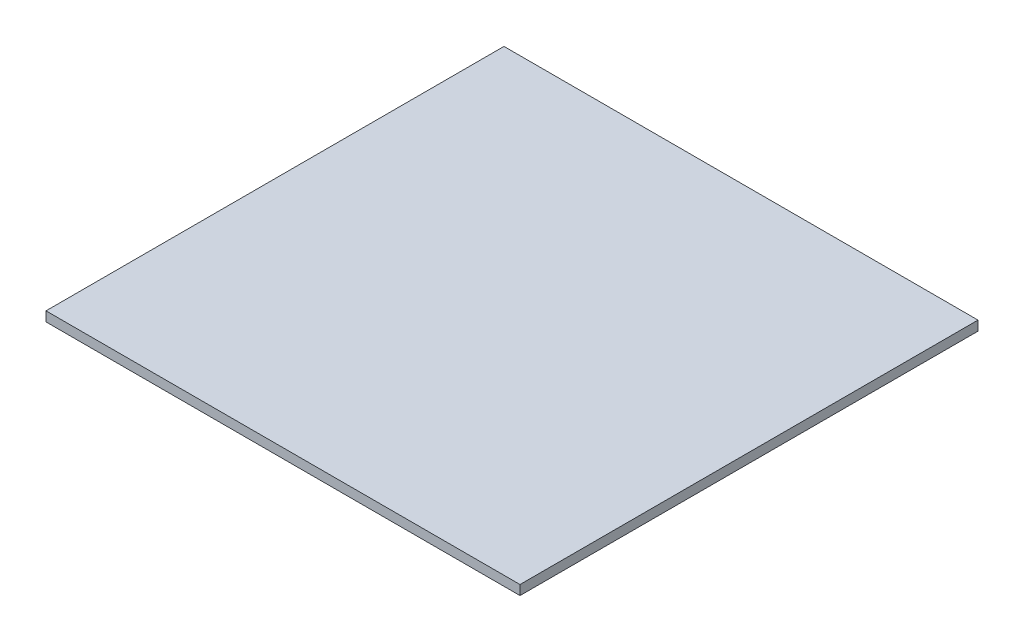
SolidWorks part; units mm, degrees
ref_plane "Front Plane" through (0, 0, 0) normal (0, 0, 1) x (1, 0, 0)
ref_plane "Top Plane" through (0, 0, 0) normal (0, 1, 0) x (1, 0, 0)
ref_plane "Right Plane" through (0, 0, 0) normal (1, 0, 0) x (0, 0, -1)
sketch "Sketch1" plane through (0, 0, 0) normal (0, 1, 0) x (1, 0, 0)
  line L1 (-469.9, -454.025) -> (469.9, -454.025)
  line L2 (-469.9, -454.025) -> (-469.9, 454.025)
  line L3 (-469.9, 454.025) -> (469.9, 454.025)
  line L4 (469.9, -454.025) -> (469.9, 454.025)
  line L5 (-469.9, -454.025) -> (469.9, 454.025) construction
  line L6 (-469.9, 454.025) -> (469.9, -454.025) construction
  point P0 (0, 0)
  dimension "D1" = 939.8
  dimension "D2" = 908.05
extrude "Boss-Extrude1" add sketch "Sketch1" along normal blind 19.05
